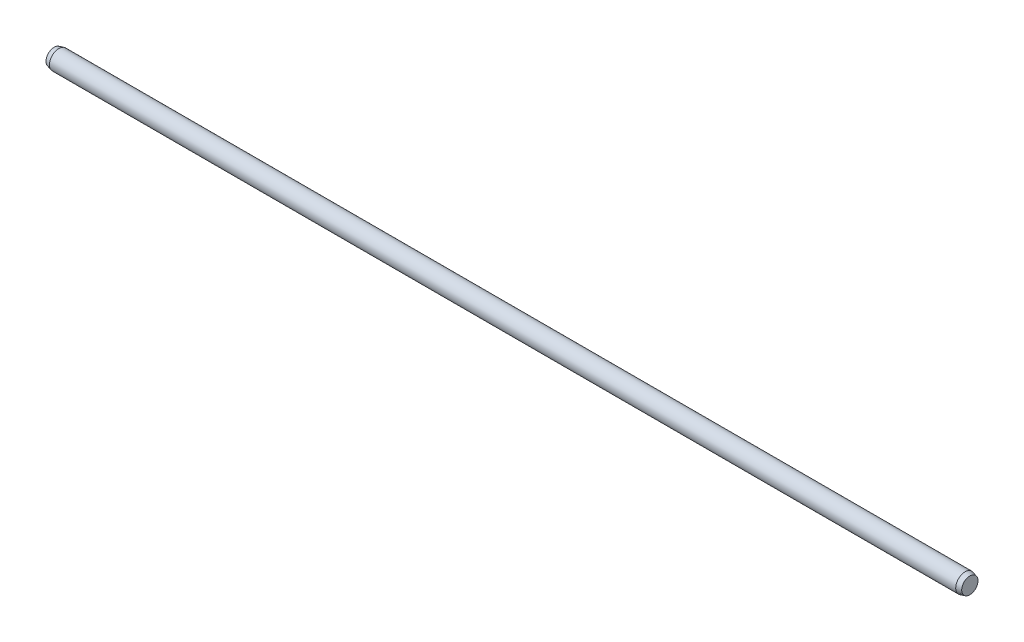
SolidWorks part; units mm, degrees
ref_plane "Front Plane" through (0, 0, 0) normal (0, 0, 1) x (1, 0, 0)
ref_plane "Top Plane" through (0, 0, 0) normal (0, 1, 0) x (1, 0, 0)
ref_plane "Right Plane" through (0, 0, 0) normal (1, 0, 0) x (0, 0, -1)
sketch "Sketch1" plane through (0, 0, 0) normal (1, 0, 0) x (0, 0, -1)
  circle A0 centre (0, 0) radius 4
  dimension "D1" = 8
extrude "Boss-Extrude1" add sketch "Sketch1" along normal mid plane 389
chamfer "Chamfer3" distance 2 angle 15 1 edges at (194.5, 0, -4)
chamfer "Chamfer4" distance 2 angle 15 1 edges at (-194.5, 0, -4)
